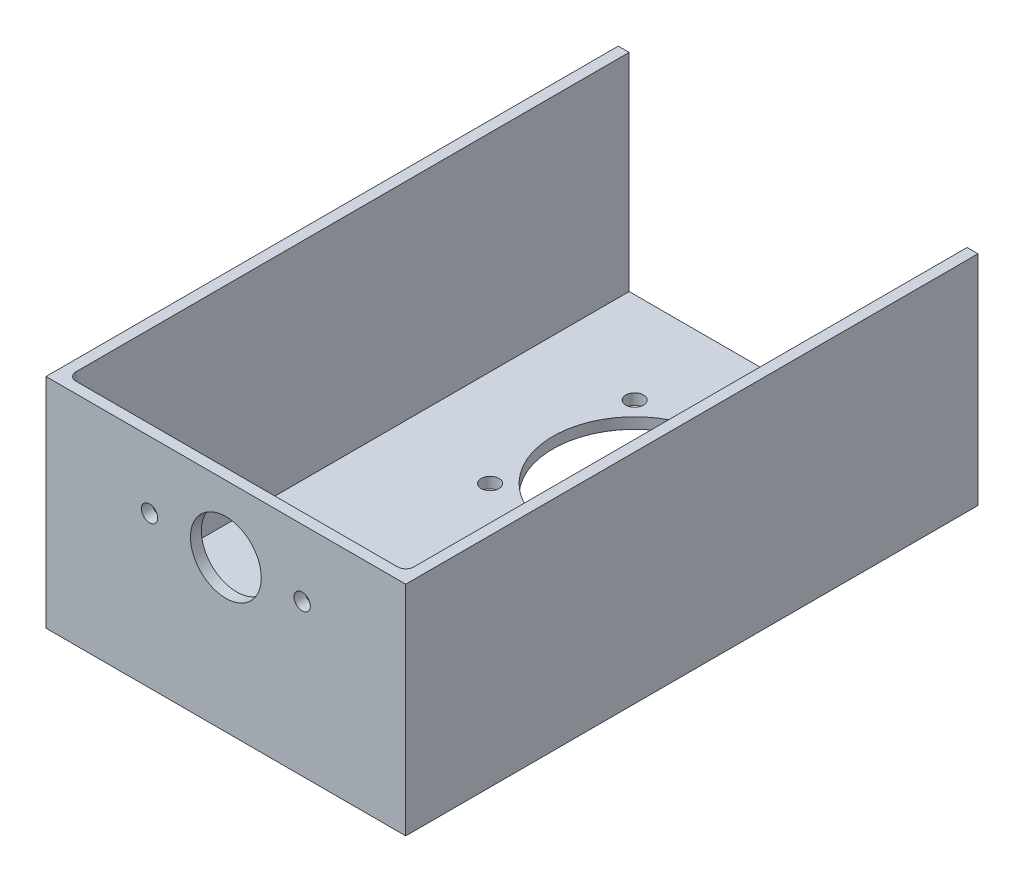
SolidWorks part; units mm, degrees
material "合金钢"
ref_plane "前视基准面" through (0, 0, 0) normal (0, 0, 1) x (1, 0, 0)
ref_plane "上视基准面" through (0, 0, 0) normal (0, 1, 0) x (1, 0, 0)
ref_plane "右视基准面" through (0, 0, 0) normal (1, 0, 0) x (0, 0, -1)
sketch "草图1" plane through (0, 0, 0) normal (0, 0, 1) x (1, 0, 0)
  line L1 (-66, -40) -> (66, -40)
  line L2 (-66, -40) -> (-66, 40)
  line L3 (-66, 40) -> (66, 40)
  line L4 (66, -40) -> (66, 40)
  line L5 (-66, -40) -> (66, 40) construction
  line L6 (-66, 40) -> (66, -40) construction
  point P0 (0, 0)
  dimension "D1" = 132
  dimension "D2" = 80
extrude "凸台-拉伸1" add sketch "草图1" against normal blind 210
sketch "草图2" plane through (0, 40, 0) normal (0, 1, 0) x (1, 0, 0)
  line L0 (-62, 4) -> (62, 4)
  line L1 (-62, 4) -> (-62, 210)
  line L2 (62, 4) -> (62, 210)
  line L3 (-62, 210) -> (62, 210)
  line L5 (0, 0) -> (0, 70.9714) construction
  line L6 (-66, 210) -> (-66, 0) construction
  line L7 (66, 210) -> (-66, 210) construction
  line L8 (66, 0) -> (-66, 0) construction
  dimension "D1" = 4
  dimension "D2" = 4
extrude "切除-拉伸1" cut sketch "草图2" against normal blind 76
sketch "草图3" plane through (0, 0, 0) normal (0, 0, 1) x (1, 0, 0)
  line L0 (0, -40) -> (0, 40) construction
  line L1 (0, 15.5) -> (-61.797, 15.5) construction
  line L2 (0, 15.5) -> (28, 15.5) construction
  line L3 (-66, -40) -> (66, -40) construction
  line L4 (66, 40) -> (-66, 40) construction
  circle A0 centre (0, 15.5) radius 13
  circle A1 centre (-28, 15.5) radius 3
  circle A2 centre (28, 15.5) radius 3
  dimension "D1" = 26
  dimension "D2" = 6
  dimension "D3" = 28
  dimension "D4" = 55.5
extrude "切除-拉伸2" cut sketch "草图3" against normal blind 10
sketch "草图4" plane through (0, -36, 0) normal (0, 1, 0) x (1, 0, 0)
  line L0 (0, 150) -> (26.5165, 176.5165) construction
  line L1 (0, 150) -> (48.6437, 150) construction
  line L2 (0, 210) -> (0, 135.1289) construction
  line L3 (62, 210) -> (-62, 210) construction
  line L4 (0, 150) -> (0, 219.8731) construction
  circle A0 centre (26.5165, 176.5165) radius 3.25
  circle A1 centre (26.5165, 123.4835) radius 3.25
  circle A2 centre (-26.5165, 123.4835) radius 3.25
  circle A3 centre (-26.5165, 176.5165) radius 3.25
  circle A4 centre (0, 150) radius 30
  dimension "D3" = 6.5
  dimension "D4" = 60
  dimension "D1" = 45
  dimension "D2" = 37.5
  dimension "D5" = 60
  dimension "D6" = 4
extrude "切除-拉伸3" cut sketch "草图4" against normal blind 10
fillet "圆角1" radius 3 2 edges at (62, 2, -4) (-62, 2, -4)
